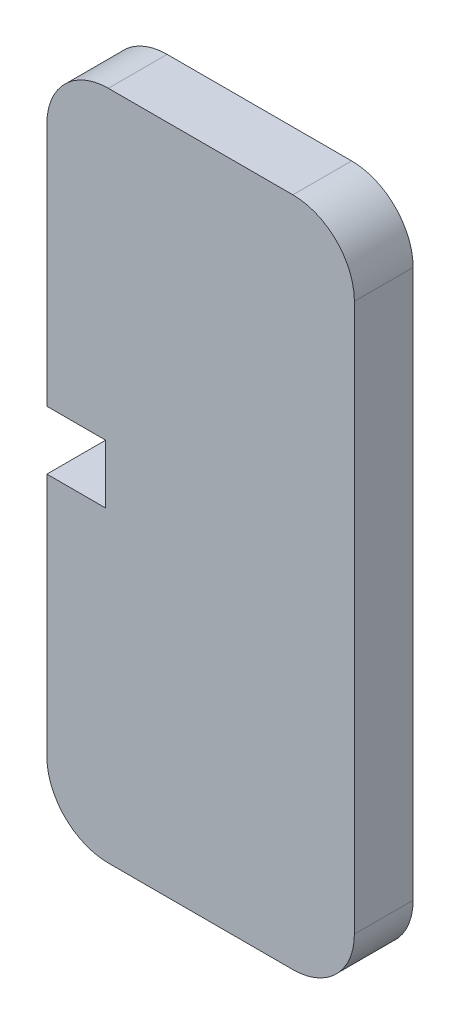
SolidWorks part; units mm, degrees
ref_plane "Front Plane" through (0, 0, 0) normal (0, 0, 1) x (1, 0, 0)
ref_plane "Top Plane" through (0, 0, 0) normal (0, 1, 0) x (1, 0, 0)
ref_plane "Right Plane" through (0, 0, 0) normal (1, 0, 0) x (0, 0, -1)
sketch "Sketch1" plane through (0, 0, 0) normal (0, 0, 1) x (1, 0, 0)
  line L0 (0.2248, 49.7752) -> (7.2248, 49.7752) construction
  line L1 (0.2248, -4.7752) -> (7.2248, -4.7752) construction
  line L2 (0.2248, 49.7752) -> (7.2248, 49.7752) construction
  line L3 (0.2248, -4.7752) -> (7.2248, -4.7752) construction
  line L4 (0.2248, 49.7752) -> (-4.5504, 49.7752) construction
  line L5 (0.2248, -4.7752) -> (-4.5504, -4.7752) construction
  line L6 (-4.5504, 44.7752) -> (-4.5504, 0.2248)
  line L7 (0.4496, -4.7752) -> (15.4496, -4.7752)
  line L8 (0.4496, 49.7752) -> (15.4496, 49.7752)
  line L9 (20.4496, 44.7752) -> (20.4496, 0.2248)
  arc A0 (-4.5504, 44.7752) -> (0.4496, 49.7752) centre (0.4496, 44.7752) cw
  arc A1 (-4.5504, 0.2248) -> (0.4496, -4.7752) centre (0.4496, 0.2248) ccw
  arc A2 (15.4496, -4.7752) -> (20.4496, 0.2248) centre (15.4496, 0.2248) ccw
  arc A3 (15.4496, 49.7752) -> (20.4496, 44.7752) centre (15.4496, 44.7752) cw
  point P16 (20.4496, -4.7752)
  point P19 (20.4496, 49.7752)
  dimension "D5" = 5
  dimension "D1" = 4.7752
  dimension "D2" = 4.7752
  dimension "D3" = 25
  dimension "D4" = 25
extrude "Boss-Extrude1" add sketch "Sketch1" along normal blind 4.7752
sketch "Sketch4" plane through (0, 0, 4.7752) normal (0, 0, 1) x (1, 0, 0)
  line L0 (-4.5504, 44.7752) -> (-4.5504, 22.5)
  line L1 (-4.5504, 44.7752) -> (-4.5504, 0.2248) construction
  line L2 (-4.5504, 22.5) -> (0.2248, 22.5) construction
  line L3 (0.2248, 20.1124) -> (0.2248, 24.8876)
  line L4 (0.2248, 24.8876) -> (-4.5504, 24.8876)
  line L5 (0.2248, 20.1124) -> (-4.5504, 20.1124)
  line L6 (-4.5504, 24.8876) -> (-4.5504, 20.1124)
  arc A0 (0.4496, 49.7752) -> (-4.5504, 44.7752) centre (0.4496, 44.7752) ccw construction
  line M6 (-4.5504, 44.7752) -> (-4.5504, 0.2248)
  dimension "D1" = 4.7752
  dimension "D2" = 2.3876
extrude "Cut-Extrude1" cut sketch "Sketch4" against normal through all contours L0 L2 L3 L4 | L2 L5 L3 M6
